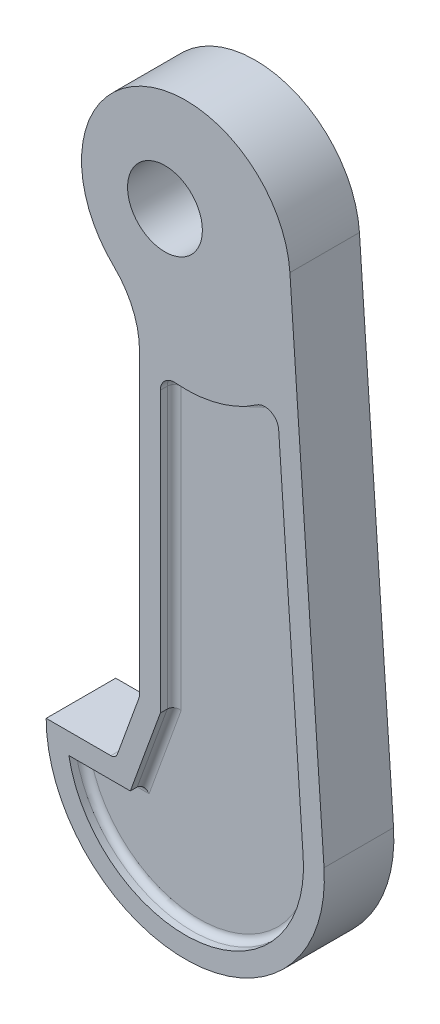
SolidWorks part; units mm, degrees
ref_plane "Front Plane" through (0, 0, 0) normal (0, 0, 1) x (1, 0, 0)
ref_plane "Top Plane" through (0, 0, 0) normal (0, 1, 0) x (1, 0, 0)
ref_plane "Right Plane" through (0, 0, 0) normal (1, 0, 0) x (0, 0, -1)
sketch "Sketch2" plane through (0, 0, 0) normal (0, 0, 1) x (1, 0, 0)
  line L0 (1.9565, -8.0001) -> (1.9565, -57.1644)
  line L1 (1.9565, -57.1644) -> (-1.4637, -66.5613)
  line L2 (-1.4637, -66.5613) -> (-11.4637, -66.5613)
  line L3 (28.4896, -65.1955) -> (23.5848, 6.463)
  line L4 (8.6198, 27.8623) -> (8.6198, -102.6393) construction
  line L5 (-11.4637, -66.5613) -> (-11.4637, 2.4387) construction
  line L6 (-11.4637, 2.4387) -> (70.6103, 2.4387) construction
  arc A0 (-11.4637, -66.5613) -> (28.4896, -65.1955) centre (8.5363, -66.5613) ccw
  arc A2 (23.5848, 6.463) -> (1.9565, -8.0001) centre (8.6198, 5.4387) ccw
  circle A3 centre (5.6198, 5.4387) radius 5.3799
  dimension "D1" = 20
  dimension "D2" = 30
  dimension "D3" = 72
  dimension "D4" = 10
  dimension "D5" = 10
  dimension "D6" = 3
  dimension "D7" = 69
  dimension "D8" = 110
extrude "Boss-Extrude1" add sketch "Sketch2" along normal mid plane 10
sketch "Sketch5" plane through (0, 0, 5) normal (0, 0, 1) x (1, 0, 0)
  line L0 (4.9565, -17.492) -> (4.9565, -57.6934)
  line L1 (4.9565, -57.6934) -> (0.637, -69.5613)
  line L2 (0.637, -69.5613) -> (-8.1969, -69.5613)
  line L3 (25.4967, -65.4004) -> (21.9707, -13.8883)
  line L12 (-3.0467, -66.5613) -> (-3.0467, 2.4387) construction
  line L13 (1.9565, -8.0001) -> (1.9565, -57.1644) construction
  line L14 (1.9565, -57.1644) -> (-1.4637, -66.5613) construction
  arc A0 (-8.1969, -69.5613) -> (25.4967, -65.4004) centre (8.5363, -66.5613) ccw
  arc A1 (18.8399, -12.3785) -> (21.9707, -13.8883) centre (19.9754, -14.0249) cw
  arc A5 (7.1229, -15.499) -> (4.9565, -17.492) centre (6.9565, -17.492) ccw
  arc A8 (7.1229, -15.499) -> (18.8399, -12.3785) centre (8.6198, 2.4387) ccw
  point P11 (0.2464, -61.8628)
  dimension "D5" = 36
  dimension "D1" = 2
  dimension "D4" = 69
  dimension "D2" = 3
  dimension "D3" = 3
extrude "Cut-Extrude1" cut sketch "Sketch5" against normal blind 2
mirror "Mirror1" about plane through (0, 0, 0) normal (0, 0, 1) of "Cut-Extrude1"
fillet "Fillet1" radius 1 18 edges at (4.9565, -37.5927, 3) (5.6024, -16.0202, 3) (13.252, -14.9551, 3) (20.8441, -12.2234, 3) (23.7337, -39.6444, 3) (5.6024, -16.0202, -3) (4.9565, -37.5927, -3) (2.7967, -63.6273, -3) (-3.78, -69.5613, -3) (10.6199, -83.4331, -3) (23.7337, -39.6444, -3) (20.8441, -12.2234, -3) (13.252, -14.9551, -3) (-3.78, -69.5613, 3) (2.7967, -63.6273, 3) (10.6199, -83.4331, 3) (-1.4637, -66.5613, 0) (1.9565, -57.1644, 0)
fillet "Fillet2" radius 12 1 edges at (1.9565, -8.0001, 0)
